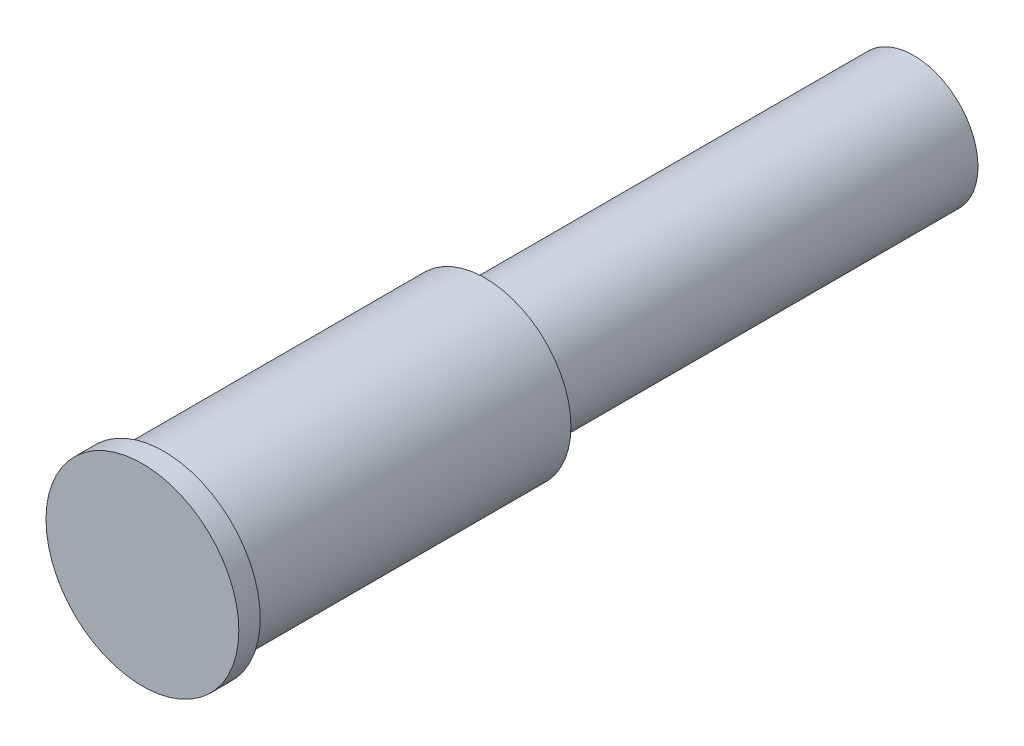
SolidWorks part; units mm, degrees
ref_plane "前视基准面" through (0, 0, 0) normal (0, 0, 1) x (1, 0, 0)
ref_plane "上视基准面" through (0, 0, 0) normal (0, 1, 0) x (1, 0, 0)
ref_plane "右视基准面" through (0, 0, 0) normal (1, 0, 0) x (0, 0, -1)
sketch "草图1" plane through (0, 0, 0) normal (0, 0, 1) x (1, 0, 0)
  circle A0 centre (0, 0) radius 3
  dimension "D1" = 6
extrude "凸台-拉伸1" add sketch "草图1" along normal blind 20
sketch "草图2" plane through (0, 0, 20) normal (0, 0, 1) x (1, 0, 0)
  circle A0 centre (0, 0) radius 4
  dimension "D1" = 8
extrude "凸台-拉伸2" add sketch "草图2" along normal blind 15
sketch "草图3" plane through (0, 0, 35) normal (0, 0, 1) x (1, 0, 0)
  circle A0 centre (0, 0) radius 4.5
  dimension "D1" = 9
extrude "凸台-拉伸3" add sketch "草图3" along normal blind 1
